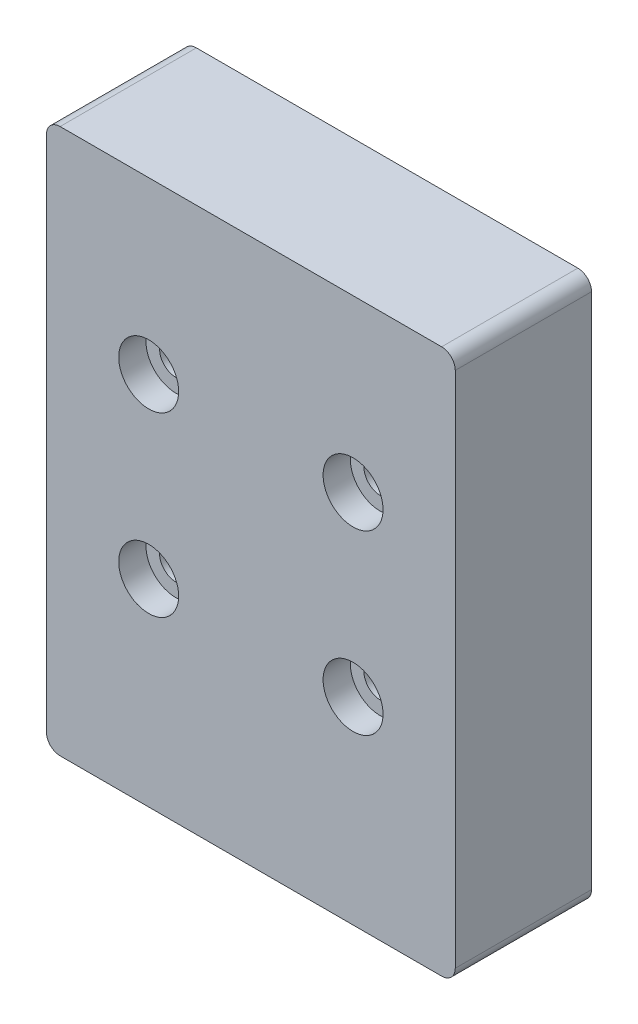
SolidWorks part; units mm, degrees
material "ABS"
ref_plane "Front Plane" through (0, 0, 0) normal (0, 0, 1) x (1, 0, 0)
ref_plane "Top Plane" through (0, 0, 0) normal (0, 1, 0) x (1, 0, 0)
ref_plane "Right Plane" through (0, 0, 0) normal (1, 0, 0) x (0, 0, -1)
sketch "Sketch1" plane through (0, 0, 0) normal (0, 0, 1) x (1, 0, 0)
  line L1 (-15, -20) -> (15, -20)
  line L2 (-15, -20) -> (-15, 20)
  line L3 (-15, 20) -> (15, 20)
  line L4 (15, -20) -> (15, 20)
  line L5 (-15, -20) -> (15, 20) construction
  line L6 (-15, 20) -> (15, -20) construction
  point P0 (0, 0)
  dimension "D1" = 40
  dimension "D2" = 30
extrude "Body" add sketch "Sketch1" along normal mid plane 10
hole_wizard "CBORE for M2 Hex Head Bolt2" positions "Sketch5" profile "Sketch6" counterbore size "M2" standard "ANSI Metric"
sketch "Sketch5" plane through (0, 0, 5) normal (0, 0, 1) x (1, 0, 0)
  line L1 (-7.5, 7.5) -> (7.5, 7.5) construction
  line L3 (15, 20) -> (-15, 20) construction
  point P0 (-7.5, 7.5)
  point P3 (7.5, 7.5)
  point P10 (0, 7.5)
  dimension "D1" = 15
  dimension "D2" = 12.5
sketch "Sketch6" plane through (-7.5, 7.5, 5) normal (1, 0, 0) x (0, -1, 0)
  line L0 (0, 0) -> (0, 10.721)
  line L1 (0, 10.721) -> (1.2, 10)
  line L2 (1.2, 10) -> (1.2, 2)
  line L3 (1.2, 2) -> (2.2, 2)
  line L4 (2.2, 2) -> (2.2, 0)
  line L5 (2.2, 0) -> (0, 0)
  line L10 (0, 10.721) -> (-1.2, 10) construction
  line L11 (0, -6.35) -> (0, 107.95) construction
  dimension "Hole Dia." = 2.4
  dimension "Hole Depth" = 10
  dimension "C'Bore Dia." = 4.4
  dimension "C'Bore Depth" = 2
  dimension "Drill Angle" = 118
pattern_linear "LPattern1" count 2 spacing 13 along (0, -1, 0) of "CBORE for M2 Hex Head Bolt2"
fillet "Fillet1" radius 1 4 edges at (15, 20, 0) (15, -20, 0) (-15, -20, 0) (-15, 20, 0)
